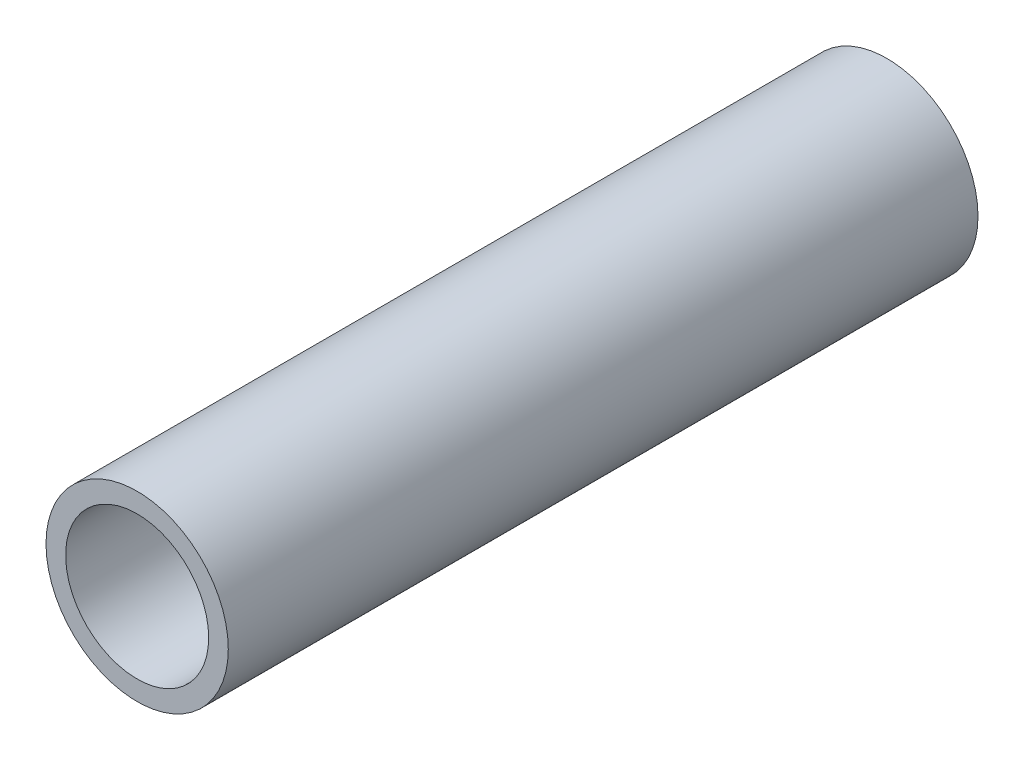
SolidWorks part; units mm, degrees
material "PVC 0.007 Plasticized"
ref_plane "Front Plane" through (0, 0, 0) normal (0, 0, 1) x (1, 0, 0)
ref_plane "Top Plane" through (0, 0, 0) normal (0, 1, 0) x (1, 0, 0)
ref_plane "Right Plane" through (0, 0, 0) normal (1, 0, 0) x (0, 0, -1)
sketch "Sketch1" plane through (0, 0, 0) normal (0, 0, 1) x (1, 0, 0)
  line L0 (10.4648, 0) -> (13.335, 0) construction
  circle A0 centre (0, 0) radius 13.335 construction
  circle A1 centre (0, 0) radius 10.4648 construction
  dimension "ID" = 20.9296
  dimension "OD" = 26.67
  dimension "Wall Thickness" = 2.8702
sketch "Sketch2" plane through (0, 0, 0) normal (1, 0, 0) x (0, 0, -1)
  line L0 (-762, 0) -> (762, 0) construction
  line L1 (-728.6625, 13.335) -> (-728.6625, -13.335) construction
  line L2 (728.6625, 13.335) -> (728.6625, -13.335) construction
  point P4 (0, 0)
  point P8 (-728.6625, 0)
  point P11 (728.6625, 0)
  dimension "Length" = 1524
  dimension "D1" = 33.3375
  dimension "D2" = 33.3375
  dimension "D3" = 26.67
sketch "Sketch3" plane through (0, 0, 0) normal (0, 0, 1) x (1, 0, 0)
  circle A0 centre (0, 0) radius 13.335
  circle A1 centre (0, 0) radius 13.335 construction
  circle A2 centre (0, 0) radius 10.4648 construction
  circle A3 centre (0, 0) radius 10.4648
extrude "Boss-Extrude1" add sketch "Sketch3" along normal up to vertex (762 mm away) and the other way up to vertex (762 mm away) up to point (0, 0, 762) other way up to point (0, 0, -762)
sketch "Sketch4" plane through (0, 0, 762) normal (0, 0, 1) x (1, 0, 0)
  circle A0 centre (0, 0) radius 10.4648 construction
  circle A1 centre (0, 0) radius 13.335 construction
  circle A2 centre (0, 0) radius 10.4648
  circle A3 centre (0, 0) radius 13.335
extrude "Cut-Extrude2" cut sketch "Sketch4" against normal offset from surface (1414.311 mm away) 109.689 contours A3 up to face at (10.4648, 0, -762)
equation "\"D1@Sketch2\"=\"OD@Sketch1\" * 1.25"
equation "\"D2@Sketch2\"=\"D1@Sketch2\""
equation "\"D3@Sketch2\"= \"OD@Sketch1\""
